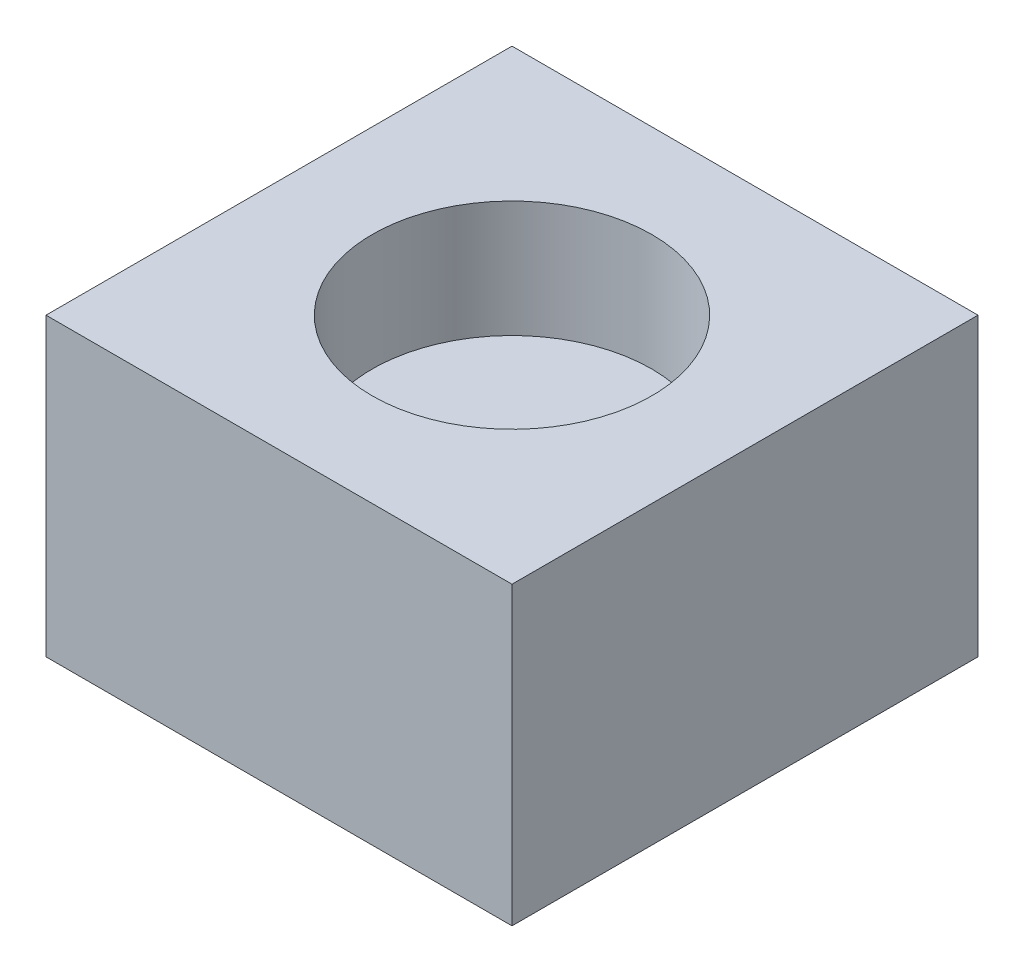
SolidWorks part; units mm, degrees
ref_plane "Front Plane" through (0, 0, 0) normal (0, 0, 1) x (1, 0, 0)
ref_plane "Top Plane" through (0, 0, 0) normal (0, 1, 0) x (1, 0, 0)
ref_plane "Right Plane" through (0, 0, 0) normal (1, 0, 0) x (0, 0, -1)
sketch "Sketch1" plane through (0, 0, 0) normal (0, 1, 0) x (1, 0, 0)
  line L1 (0, 0) -> (10, 0)
  line L2 (0, 0) -> (0, 10)
  line L3 (0, 10) -> (10, 10)
  line L4 (10, 0) -> (10, 10)
  point P7 (5.0466, 5.0271)
  point P8 (0, 0)
  dimension "D1" = 10
  dimension "D2" = 10
extrude "Boss-Extrude1" add sketch "Sketch1" along normal blind 6.35
sketch "Sketch2" plane through (0, 6.35, 0) normal (0, 1, 0) x (1, 0, 0)
  line L0 (10, 10) -> (0, 10) construction
  line L1 (10, 0) -> (10, 10) construction
  circle A0 centre (5, 5) radius 3
  point P4 (5, 10)
  point P7 (10, 5)
  dimension "D1" = 6
extrude "Cut-Extrude1" cut sketch "Sketch2" against normal blind 2.5
